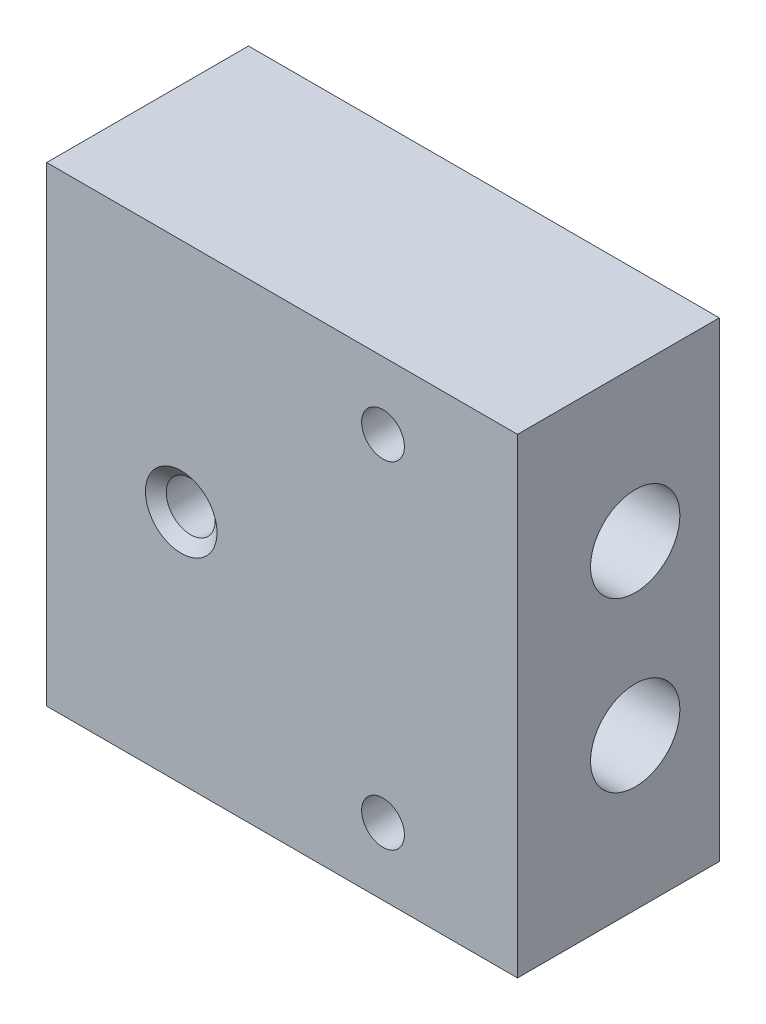
SolidWorks part; units mm, degrees
ref_plane "Front Plane" through (0, 0, 0) normal (0, 0, 1) x (1, 0, 0)
ref_plane "Top Plane" through (0, 0, 0) normal (0, 1, 0) x (1, 0, 0)
ref_plane "Right Plane" through (0, 0, 0) normal (1, 0, 0) x (0, 0, -1)
sketch "Sketch1" plane through (0, 0, 0) normal (0, 0, 1) x (1, 0, 0)
  line L1 (-22.225, -22.225) -> (22.225, -22.225)
  line L2 (-22.225, -22.225) -> (-22.225, 22.225)
  line L3 (-22.225, 22.225) -> (22.225, 22.225)
  line L4 (22.225, -22.225) -> (22.225, 22.225)
  line L5 (-22.225, -22.225) -> (22.225, 22.225) construction
  line L6 (-22.225, 22.225) -> (22.225, -22.225) construction
  point P0 (0, 0)
  dimension "D1" = 44.45
  dimension "D2" = 44.45
extrude "Boss-Extrude1" add sketch "Sketch1" along normal blind 19.05 contours L2 L3 L4 L1
hole_wizard "#12-28 Tapped Hole1" positions "Sketch4" profile "Sketch5" tap size "#12-28" standard "ANSI Inch"
sketch "Sketch4" plane through (0, 0, 19.05) normal (0, 0, 1) x (1, 0, 0)
  point P0 (-9.525, 0)
  point P4 (-12.2046, -3.5124)
  dimension "D1" = 9.525
sketch "Sketch5" plane through (-9.525, 0, 19.05) normal (1, 0, 0) x (0, -1, 0)
  line L0 (0, 0) -> (0, 12.8188)
  line L1 (0, 12.8188) -> (2.3114, 11.43)
  line L2 (2.3114, 11.43) -> (2.3114, 0.8952)
  line L3 (2.3114, 0.8952) -> (3.3782, 0)
  line L5 (3.3782, 0) -> (0, 0)
  line L6 (-2.3114, 0.8952) -> (-3.3782, 0) construction
  line L10 (0, 12.8188) -> (-2.3114, 11.43) construction
  line L11 (0, -6.35) -> (0, 107.95) construction
  dimension "Tap Drill Dia." = 4.6228
  dimension "Tap Drill Depth" = 11.43
  dimension "Near C'Sink Dia." = 6.7564
  dimension "Near C'Sink Angle" = 100
  dimension "Drill Angle" = 118
cosmetic thread "Hole Thread1" parameters "D1"=6.35, "D2"=4.699
hole_wizard "Pipe Tap Drill for 1/8 Tap1" positions "Sketch11" profile "Sketch10" hole size "1/8" standard "ANSI Inch"
sketch "Sketch11" plane through (22.225, 0, 0) normal (1, 0, 0) x (0, 0, -1)
  line L0 (-7.9375, 22.225) -> (-7.9375, -22.225) construction
  line L4 (0, 0) -> (-19.05, 0) construction
  line L5 (-19.05, -22.225) -> (-19.05, 22.225) construction
  line L6 (0, -22.225) -> (0, 22.225) construction
  point P0 (-7.9375, 7.9375)
  point P2 (-7.9375, -7.9375)
  dimension "D1" = 7.9375
  dimension "D2" = 7.9375
  dimension "D3" = 7.9375
sketch "Sketch10" plane through (22.225, 7.9375, 7.9375) normal (0, 1, 0) x (0, 0, -1)
  line L0 (0, 0) -> (0, 37.5855)
  line L1 (0, 37.5855) -> (4.2164, 35.052)
  line L2 (4.2164, 35.052) -> (4.2164, 0)
  line L5 (4.2164, 0) -> (0, 0)
  line L10 (0, 37.5855) -> (-4.2164, 35.052) construction
  line L11 (0, -6.35) -> (0, 107.95) construction
  dimension "Hole Dia." = 8.4328
  dimension "Hole Depth" = 35.052
  dimension "Drill Angle" = 118
hole_wizard "#10-32 Tapped Hole1" positions "Sketch13" profile "Sketch14" tap size "#10-32" standard "ANSI Inch" end condition through all
sketch "Sketch13" plane through (0, 0, 19.05) normal (0, 0, 1) x (1, 0, 0)
  line L0 (22.225, 0) -> (0, 0) construction
  line L1 (22.225, -22.225) -> (22.225, 22.225) construction
  line L3 (9.525, 22.225) -> (9.525, -22.225) construction
  line L4 (-22.225, 22.225) -> (22.225, 22.225) construction
  line L5 (-22.225, -22.225) -> (22.225, -22.225) construction
  point P0 (9.525, 15.875)
  point P2 (9.525, -15.875)
  point P20 (14.3222, 12.5319)
  point P21 (14.3222, -14.4235)
  dimension "D1" = 15.875
  dimension "D2" = 15.875
  dimension "D3" = 9.525
sketch "Sketch14" plane through (9.525, 15.875, 19.05) normal (1, 0, 0) x (0, -1, 0)
  line L0 (0, 0) -> (0, 19.05)
  line L1 (0, 19.05) -> (2.0193, 19.05)
  line L2 (2.0193, 19.05) -> (2.0193, 0)
  line L5 (2.0193, 0) -> (0, 0)
  line L11 (0, -6.35) -> (0, 107.95) construction
  dimension "Thru Tap Drill Dia." = 4.0386
  dimension "Thru Tap Drill Depth" = 19.05
cosmetic thread "Hole Thread2" parameters "D2"=4.826
cosmetic thread "Hole Thread3" parameters "D2"=4.826
hole_wizard "3/8-24 Tapped Hole1" positions "Sketch17" profile "Sketch18" tap size "3/8-24" standard "ANSI Inch"
sketch "Sketch17" plane through (0, 0, 0) normal (0, 0, -1) x (-1, 0, 0)
  point P0 (9.525, 0)
  point P7 (12.126, -2.813)
sketch "Sketch18" plane through (-9.525, 0, 0) normal (1, 0, 0) x (0, 1, 0)
  line L0 (0, 0) -> (0, 12.1855)
  line L1 (0, 12.1855) -> (4.2164, 9.652)
  line L2 (4.2164, 9.652) -> (4.2164, 0)
  line L5 (4.2164, 0) -> (0, 0)
  line L10 (0, 12.1855) -> (-4.2164, 9.652) construction
  line L11 (0, -6.35) -> (0, 107.95) construction
  dimension "Tap Drill Dia." = 8.4328
  dimension "Tap Drill Depth" = 9.652
  dimension "Drill Angle" = 118
cosmetic thread "Hole Thread4" parameters "D1"=6.35, "D2"=9.525
equation "\"D2@Sketch11\"=\"D1@Sketch11\""
equation "\"D2@Sketch13\"=\"D1@Sketch13\""
